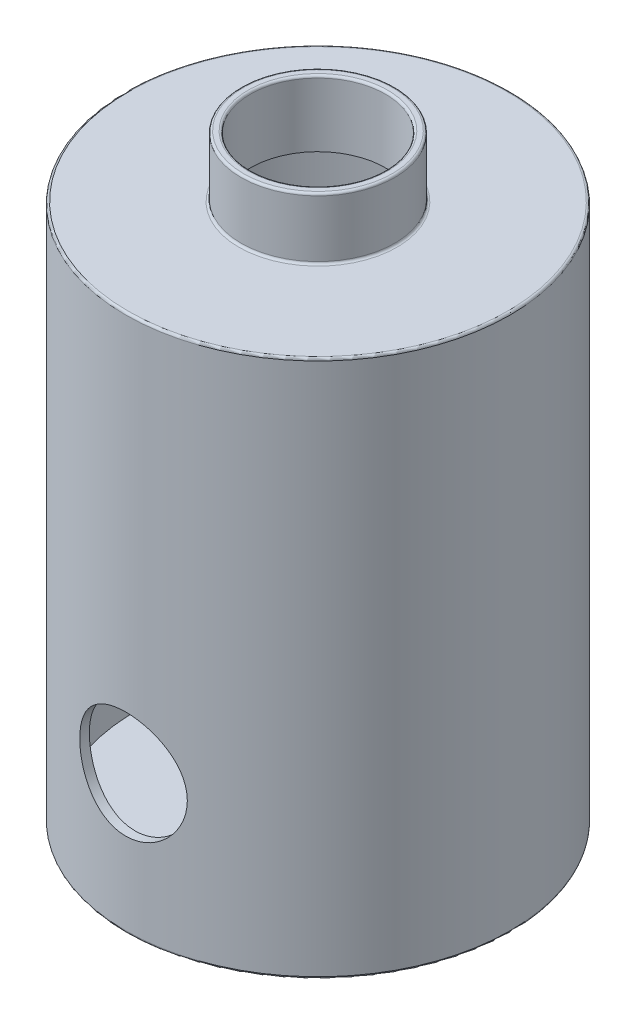
SolidWorks part; units mm, degrees
ref_plane "Front Plane" through (0, 0, 0) normal (0, 0, 1) x (1, 0, 0)
ref_plane "Top Plane" through (0, 0, 0) normal (0, 1, 0) x (1, 0, 0)
ref_plane "Right Plane" through (0, 0, 0) normal (1, 0, 0) x (0, 0, -1)
sketch "Sketch1" plane through (0, 0, 0) normal (0, 1, 0) x (1, 0, 0)
  circle A0 centre (0, 0) radius 62.5
  dimension "D1" = 125
extrude "Boss-Extrude1" add sketch "Sketch1" along normal blind 175
sketch "Sketch2" plane through (0, 175, 0) normal (0, 1, 0) x (1, 0, 0)
  circle A0 centre (0, 0) radius 59.5
extrude "Cut-Extrude1" cut sketch "Sketch2" against normal blind 172 from offset 1.5 offset against normal yes
sketch "Sketch3" plane through (0, 175, 0) normal (0, 1, 0) x (1, 0, 0)
  circle A0 centre (0, 0) radius 25
extrude "Boss-Extrude2" add sketch "Sketch3" along normal blind 20
sketch "Sketch4" plane through (0, 195, 0) normal (0, 1, 0) x (1, 0, 0)
  circle A0 centre (0, 0) radius 22
extrude "Cut-Extrude2" cut sketch "Sketch4" against normal blind 30
fillet "Fillet1" radius 0.75 5 edges at (0, 0, 62.5) (0, 175, 62.5) (0, 175, 25) (0, 195, 25) (0, 195, 22)
sketch "Sketch5" plane through (0, 0, 0) normal (0, 0, 1) x (1, 0, 0)
  circle A0 centre (0, 44.8952) radius 17.5
extrude "Cut-Extrude3" cut sketch "Sketch5" against normal blind 70 and the other way through all contours A0
